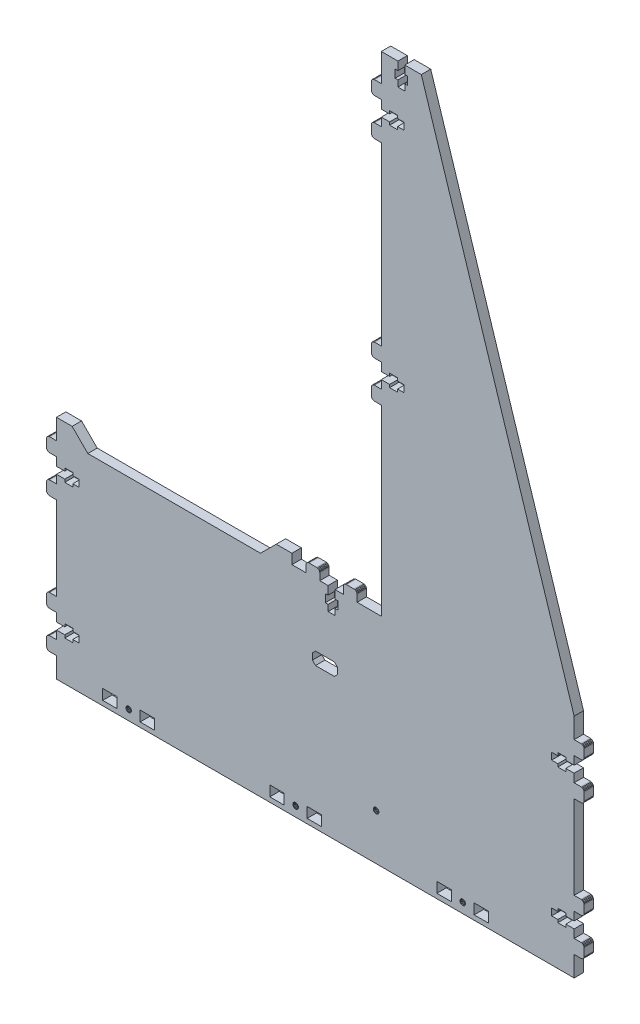
SolidWorks part; units mm, degrees
material "Maple"
ref_plane "Front Plane" through (0, 0, 0) normal (0, 0, 1) x (1, 0, 0)
ref_plane "Top Plane" through (0, 0, 0) normal (0, 1, 0) x (1, 0, 0)
ref_plane "Right Plane" through (0, 0, 0) normal (1, 0, 0) x (0, 0, -1)
sketch "Sketch1" plane through (0, 0, 0) normal (0, 0, 1) x (1, 0, 0)
  line L3039 (22.6213, 221.741) -> (22.6213, 217.341)
  line L3040 (-188.3287, 59.791) -> (-193.4287, 59.791)
  line L3041 (8.2713, 366.6083) -> (13.5713, 366.6083)
  line L3042 (18.6713, 215.541) -> (13.5713, 215.541)
  line L3043 (18.8713, 384.0909) -> (23.2713, 384.0909)
  line L3044 (18.8713, 398.4409) -> (18.8713, 393.1409)
  line L3045 (120.7712, 67.791) -> (125.8712, 67.791)
  line L3046 (125.8712, 67.791) -> (125.8712, 65.991)
  line L3047 (-193.4287, 61.591) -> (-198.7287, 61.591)
  line L3048 (-198.7287, 56.291) -> (-198.7287, 61.591)
  line L3049 (-184.3787, 61.591) -> (-188.3287, 61.591)
  line L3050 (-188.3287, 61.591) -> (-188.3287, 59.791)
  line L3051 (22.6213, 366.6083) -> (22.6213, 362.2083)
  line L3052 (13.5713, 217.341) -> (8.2713, 217.341)
  line L3053 (8.2713, 212.041) -> (3.9713, 212.041)
  line L3054 (120.7712, 59.791) -> (120.7712, 61.591)
  line L3055 (120.7712, 61.591) -> (116.8212, 61.591)
  line L3056 (25.0713, 388.0409) -> (25.0713, 393.1409)
  line L3057 (17.0713, 393.1409) -> (17.0713, 388.0409)
  line L3058 (23.2713, 388.0409) -> (25.0713, 388.0409)
  line L3059 (-193.4287, 67.791) -> (-188.3287, 67.791)
  line L3060 (-188.3287, 67.791) -> (-188.3287, 65.991)
  line L3061 (23.2713, 398.4409) -> (33.7796, 398.4409)
  line L3062 (131.1712, 47.491) -> (135.5212, 47.491)
  line L3063 (18.6713, 366.6083) -> (22.6213, 366.6083)
  line L3064 (18.6713, 217.341) -> (18.6713, 215.541)
  line L3065 (-198.7287, -51.459) -> (-198.7287, -38.459)
  line L3066 (18.6713, 368.4083) -> (18.6713, 366.6083)
  line L3067 (8.2713, 362.2083) -> (8.2713, 356.9083)
  line L3068 (13.5713, 368.4083) -> (18.6713, 368.4083)
  line L3069 (23.2713, 384.0909) -> (23.2713, 388.0409)
  line L3070 (116.8212, 65.991) -> (120.7712, 65.991)
  line L3071 (120.7712, 65.991) -> (120.7712, 67.791)
  line L3072 (8.2713, 380.7083) -> (3.9713, 380.7083)
  line L3073 (13.5713, 223.541) -> (18.6713, 223.541)
  line L3074 (131.1712, 61.591) -> (125.8712, 61.591)
  line L3075 (22.6213, 217.341) -> (18.6713, 217.341)
  line L3076 (13.5713, 366.6083) -> (13.5713, 368.4083)
  line L3077 (-198.7287, 80.091) -> (-198.7287, 93.041)
  line L3078 (-193.4287, 59.791) -> (-193.4287, 61.591)
  line L3079 (13.5713, 362.2083) -> (8.2713, 362.2083)
  line L3080 (8.2713, 356.9083) -> (3.9713, 356.9083)
  line L3081 (131.1712, 56.291) -> (131.1712, 61.591)
  line L3082 (116.8212, 61.591) -> (116.8212, 65.991)
  line L3083 (8.2713, 221.741) -> (13.5713, 221.741)
  line L3084 (8.2713, 235.841) -> (3.9713, 235.841)
  line L3085 (8.2713, 398.4409) -> (18.8713, 398.4409)
  line L3086 (25.0713, 393.1409) -> (23.2713, 393.1409)
  line L3087 (23.2713, 393.1409) -> (23.2713, 398.4409)
  line L3088 (13.5713, 215.541) -> (13.5713, 217.341)
  line L3089 (18.6713, 223.541) -> (18.6713, 221.741)
  line L3090 (-198.7287, 56.291) -> (-203.0787, 56.291)
  line L3091 (-184.3787, 65.991) -> (-184.3787, 61.591)
  line L3092 (8.2713, 217.341) -> (8.2713, 212.041)
  line L3093 (22.6213, 362.2083) -> (18.6713, 362.2083)
  line L3094 (13.5713, 360.4083) -> (13.5713, 362.2083)
  line L3095 (-198.7287, 65.991) -> (-198.7287, 71.291)
  line L3096 (131.1712, 65.991) -> (131.1712, 71.291)
  line L3097 (131.1712, 71.291) -> (135.5212, 71.291)
  line L3098 (131.1712, 47.491) -> (131.1712, -5.859)
  line L3099 (125.8712, 61.591) -> (125.8712, 59.791)
  line L3100 (125.8712, 59.791) -> (120.7712, 59.791)
  line L3101 (131.1712, 80.091) -> (131.1712, 93.041)
  line L3102 (8.2713, 371.9083) -> (8.2713, 366.6083)
  line L3103 (33.7796, 398.4409) -> (131.1712, 93.041)
  line L3104 (18.6713, 221.741) -> (22.6213, 221.741)
  line L3105 (-198.7287, 65.991) -> (-193.4287, 65.991)
  line L3106 (18.8713, 388.0409) -> (18.8713, 384.0909)
  line L3107 (8.2713, 227.041) -> (8.2713, 221.741)
  line L3108 (-188.3287, 65.991) -> (-184.3787, 65.991)
  line L3109 (-48.019, -45.6253) -> (-48.0804, -45.159)
  line L3110 (17.0713, 388.0409) -> (18.8713, 388.0409)
  line L3111 (18.8713, 393.1409) -> (17.0713, 393.1409)
  line L3112 (-193.4287, 65.991) -> (-193.4287, 67.791)
  line L3113 (-198.7287, 80.091) -> (-203.0787, 80.091)
  line L3114 (13.5713, 221.741) -> (13.5713, 223.541)
  line L3115 (125.8712, 65.991) -> (131.1712, 65.991)
  line L3116 (-46.745, -43.4186) -> (-46.2787, -43.3572)
  line L3117 (18.6713, 362.2083) -> (18.6713, 360.4083)
  line L3118 (18.6713, 360.4083) -> (13.5713, 360.4083)
  line L3119 (-25.6287, 86.741) -> (-25.6287, 81.441)
  line L3120 (-21.2287, 72.391) -> (-21.2287, 76.341)
  line L3121 (-21.2287, 81.441) -> (-21.2287, 86.741)
  line L3122 (-15.9287, 86.741) -> (-15.9287, 91.091)
  line L3123 (-48.672, 93.041) -> (-48.672, 86.741)
  line L3124 (-25.6287, 72.391) -> (-21.2287, 72.391)
  line L3125 (-21.2287, 76.341) -> (-19.4287, 76.341)
  line L3126 (-27.4287, 76.341) -> (-25.6287, 76.341)
  line L3127 (-25.6287, 81.441) -> (-27.4287, 81.441)
  line L3128 (-25.6287, 86.741) -> (-30.9287, 86.741)
  line L3129 (-39.7287, 86.741) -> (-39.7287, 91.091)
  line L3130 (-25.6287, 76.341) -> (-25.6287, 72.391)
  line L3131 (-39.7287, 86.741) -> (-48.672, 86.741)
  line L3132 (-19.4287, 81.441) -> (-21.2287, 81.441)
  line L3133 (-15.9287, 86.741) -> (-21.2287, 86.741)
  line L3134 (-27.4287, 81.441) -> (-27.4287, 76.341)
  line L3135 (-19.4287, 76.341) -> (-19.4287, 81.441)
  line L3136 (-48.672, 93.041) -> (-58.672, 93.041)
  line L3137 (3.9713, 212.041) -> (3.4536, 211.9728)
  line L3138 (3.4536, 211.9728) -> (2.9713, 211.773)
  line L3139 (2.9713, 211.773) -> (2.5571, 211.4552)
  line L3140 (2.5571, 211.4552) -> (2.2392, 211.041)
  line L3141 (2.2392, 211.041) -> (2.0394, 210.5586)
  line L3142 (1.9713, 210.041) -> (1.9713, 205.241)
  line L3143 (2.0394, 210.5586) -> (1.9713, 210.041)
  line L3144 (3.9713, 203.241) -> (8.2713, 203.241)
  line L3145 (3.9713, 203.241) -> (3.4536, 203.3091)
  line L3146 (3.4536, 203.3091) -> (2.9713, 203.5089)
  line L3147 (-188.7287, 93.041) -> (-198.7287, 93.041)
  line L3148 (-188.7287, 93.041) -> (-178.7287, 83.041)
  line L3149 (-178.7287, 83.041) -> (-68.672, 83.041)
  line L3150 (-68.672, 83.041) -> (-58.672, 93.041)
  line L3151 (2.9713, 203.5089) -> (2.5571, 203.8268)
  line L3152 (2.5571, 203.8268) -> (2.2392, 204.241)
  line L3153 (2.2392, 204.241) -> (2.0394, 204.7233)
  line L3154 (2.0394, 204.7233) -> (1.9713, 205.241)
  line L3155 (3.9713, 235.841) -> (3.4536, 235.7728)
  line L3156 (3.4536, 235.7728) -> (2.9713, 235.573)
  line L3157 (2.9713, 235.573) -> (2.5571, 235.2552)
  line L3158 (2.5571, 235.2552) -> (2.2392, 234.841)
  line L3159 (2.2392, 234.841) -> (2.0394, 234.3586)
  line L3160 (1.9713, 233.841) -> (1.9713, 229.041)
  line L3161 (2.0394, 234.3586) -> (1.9713, 233.841)
  line L3162 (3.9713, 356.9083) -> (3.4536, 356.8401)
  line L3163 (3.4536, 356.8401) -> (2.9713, 356.6403)
  line L3164 (2.9713, 356.6403) -> (2.5571, 356.3225)
  line L3165 (2.5571, 356.3225) -> (2.2392, 355.9083)
  line L3166 (2.2392, 355.9083) -> (2.0394, 355.4259)
  line L3167 (1.9713, 354.9083) -> (1.9713, 350.1083)
  line L3168 (2.0394, 355.4259) -> (1.9713, 354.9083)
  line L3169 (3.9713, 348.1083) -> (8.2713, 348.1083)
  line L3170 (3.9713, 348.1083) -> (3.4536, 348.1764)
  line L3171 (3.4536, 348.1764) -> (2.9713, 348.3762)
  line L3172 (2.9713, 348.3762) -> (2.5571, 348.6941)
  line L3173 (2.5571, 348.6941) -> (2.2392, 349.1083)
  line L3174 (2.2392, 349.1083) -> (2.0394, 349.5906)
  line L3175 (2.0394, 349.5906) -> (1.9713, 350.1083)
  line L3176 (-205.0787, 78.091) -> (-205.0787, 73.291)
  line L3177 (-205.0787, 78.091) -> (-205.0105, 78.6086)
  line L3178 (-205.0105, 78.6086) -> (-204.8107, 79.091)
  line L3179 (-204.8107, 79.091) -> (-204.4929, 79.5052)
  line L3180 (-204.4929, 79.5052) -> (-204.0787, 79.8231)
  line L3181 (-204.0787, 79.8231) -> (-203.5963, 80.0229)
  line L3182 (-203.5963, 80.0229) -> (-203.0787, 80.091)
  line L3183 (-203.0787, 56.291) -> (-203.5963, 56.2229)
  line L3184 (-203.5963, 56.2229) -> (-204.0787, 56.0231)
  line L3185 (-204.0787, 56.0231) -> (-204.4929, 55.7052)
  line L3186 (-204.4929, 55.7052) -> (-204.8107, 55.291)
  line L3187 (-204.8107, 55.291) -> (-205.0105, 54.8087)
  line L3188 (-205.0787, 54.291) -> (-205.0787, 49.491)
  line L3189 (-205.0105, 54.8087) -> (-205.0787, 54.291)
  line L3190 (-203.0787, 47.491) -> (-198.7287, 47.491)
  line L3191 (-203.0787, 47.491) -> (-203.5963, 47.5592)
  line L3192 (-203.5963, 47.5592) -> (-204.0787, 47.759)
  line L3193 (-204.0787, 47.759) -> (-204.4929, 48.0768)
  line L3194 (-204.4929, 48.0768) -> (-204.8107, 48.491)
  line L3195 (-204.8107, 48.491) -> (-205.0105, 48.9734)
  line L3196 (-205.0105, 48.9734) -> (-205.0787, 49.491)
  line L3197 (3.9713, 380.7083) -> (3.4536, 380.6401)
  line L3198 (3.4536, 380.6401) -> (2.9713, 380.4403)
  line L3199 (2.9713, 380.4403) -> (2.5571, 380.1225)
  line L3200 (2.5571, 380.1225) -> (2.2392, 379.7083)
  line L3201 (2.2392, 379.7083) -> (2.0394, 379.2259)
  line L3202 (1.9713, 378.7083) -> (1.9713, 373.9083)
  line L3203 (2.0394, 379.2259) -> (1.9713, 378.7083)
  line L3204 (3.9713, 371.9083) -> (8.2713, 371.9083)
  line L3205 (3.9713, 371.9083) -> (3.4536, 371.9764)
  line L3206 (3.4536, 371.9764) -> (2.9713, 372.1762)
  line L3207 (2.9713, 372.1762) -> (2.5571, 372.4941)
  line L3208 (2.5571, 372.4941) -> (2.2392, 372.9083)
  line L3209 (2.2392, 372.9083) -> (2.0394, 373.3906)
  line L3210 (2.0394, 373.3906) -> (1.9713, 373.9083)
  line L3211 (3.9713, 227.041) -> (8.2713, 227.041)
  line L3212 (3.9713, 227.041) -> (3.4536, 227.1091)
  line L3213 (3.4536, 227.1091) -> (2.9713, 227.3089)
  line L3214 (2.9713, 227.3089) -> (2.5571, 227.6267)
  line L3215 (2.5571, 227.6267) -> (2.2392, 228.041)
  line L3216 (2.2392, 228.041) -> (2.0394, 228.5233)
  line L3217 (2.0394, 228.5233) -> (1.9713, 229.041)
  line L3218 (-203.0787, 71.291) -> (-198.7287, 71.291)
  line L3219 (-203.0787, 71.291) -> (-203.5963, 71.3592)
  line L3220 (-203.5963, 71.3592) -> (-204.0787, 71.559)
  line L3221 (-204.0787, 71.559) -> (-204.4929, 71.8768)
  line L3222 (-204.4929, 71.8768) -> (-204.8107, 72.291)
  line L3223 (-204.8107, 72.291) -> (-205.0105, 72.7734)
  line L3224 (-205.0105, 72.7734) -> (-205.0787, 73.291)
  line L3225 (135.5212, 71.291) -> (136.0389, 71.3592)
  line L3226 (136.0389, 71.3592) -> (136.5212, 71.559)
  line L3227 (136.5212, 71.559) -> (136.9354, 71.8768)
  line L3228 (136.9354, 71.8768) -> (137.2533, 72.291)
  line L3229 (137.2533, 72.291) -> (137.4531, 72.7734)
  line L3230 (137.5212, 73.291) -> (137.5212, 78.091)
  line L3231 (137.4531, 72.7734) -> (137.5212, 73.291)
  line L3232 (135.5212, 80.091) -> (131.1712, 80.091)
  line L3233 (135.5212, 80.091) -> (136.0389, 80.0229)
  line L3234 (136.0389, 80.0229) -> (136.5212, 79.8231)
  line L3235 (136.5212, 79.8231) -> (136.9354, 79.5052)
  line L3236 (136.9354, 79.5052) -> (137.2533, 79.091)
  line L3237 (137.2533, 79.091) -> (137.4531, 78.6087)
  line L3238 (137.4531, 78.6087) -> (137.5212, 78.091)
  line L3239 (-30.9287, 91.091) -> (-30.9287, 86.741)
  line L3240 (-30.9287, 91.091) -> (-30.9969, 91.6086)
  line L3241 (-30.9969, 91.6086) -> (-31.1967, 92.091)
  line L3242 (-31.1967, 92.091) -> (-31.5145, 92.5052)
  line L3243 (-31.5145, 92.5052) -> (-31.9287, 92.8231)
  line L3244 (-31.9287, 92.8231) -> (-32.4111, 93.0229)
  line L3245 (-32.4111, 93.0229) -> (-32.9287, 93.091)
  line L3246 (-15.9287, 91.091) -> (-15.8606, 91.6086)
  line L3247 (-15.8606, 91.6086) -> (-15.6608, 92.091)
  line L3248 (-15.6608, 92.091) -> (-15.3429, 92.5052)
  line L3249 (-15.3429, 92.5052) -> (-14.9287, 92.8231)
  line L3250 (-14.9287, 92.8231) -> (-14.4464, 93.0229)
  line L3251 (-13.9287, 93.091) -> (-9.1287, 93.091)
  line L3252 (-14.4464, 93.0229) -> (-13.9287, 93.091)
  line L3253 (-39.7287, 91.091) -> (-39.6606, 91.6086)
  line L3254 (-39.6606, 91.6086) -> (-39.4608, 92.091)
  line L3255 (-39.4608, 92.091) -> (-39.1429, 92.5052)
  line L3256 (-39.1429, 92.5052) -> (-38.7287, 92.8231)
  line L3257 (-38.7287, 92.8231) -> (-38.2463, 93.0229)
  line L3258 (-37.7287, 93.091) -> (-32.9287, 93.091)
  line L3259 (-38.2463, 93.0229) -> (-37.7287, 93.091)
  line L3260 (-7.1287, 91.091) -> (-7.1287, 86.741)
  line L3261 (-7.1287, 91.091) -> (-7.1969, 91.6086)
  line L3262 (-7.1969, 91.6086) -> (-7.3967, 92.091)
  line L3263 (-7.3967, 92.091) -> (-7.7145, 92.5052)
  line L3264 (-7.7145, 92.5052) -> (-8.1287, 92.8231)
  line L3265 (-8.1287, 92.8231) -> (-8.6111, 93.0229)
  line L3266 (-8.6111, 93.0229) -> (-9.1287, 93.091)
  line L3267 (135.5212, 47.491) -> (136.0389, 47.5592)
  line L3268 (136.0389, 47.5592) -> (136.5212, 47.759)
  line L3269 (136.5212, 47.759) -> (136.9354, 48.0768)
  line L3270 (136.9354, 48.0768) -> (137.2533, 48.491)
  line L3271 (137.2533, 48.491) -> (137.4531, 48.9734)
  line L3272 (137.5212, 49.491) -> (137.5212, 54.291)
  line L3273 (137.4531, 48.9734) -> (137.5212, 49.491)
  line L3274 (135.5212, 56.291) -> (131.1712, 56.291)
  line L3275 (135.5212, 56.291) -> (136.0389, 56.2229)
  line L3276 (136.0389, 56.2229) -> (136.5212, 56.0231)
  line L3277 (136.5212, 56.0231) -> (136.9354, 55.7052)
  line L3278 (136.9354, 55.7052) -> (137.2533, 55.291)
  line L3279 (137.2533, 55.291) -> (137.4531, 54.8087)
  line L3280 (137.4531, 54.8087) -> (137.5212, 54.291)
  line L3281 (61.7316, -46.0598) -> (61.4453, -46.433)
  line L3282 (-53.5787, -48.459) -> (-62.7787, -48.459)
  line L3283 (52.8713, -41.859) -> (52.8713, -48.459)
  line L3284 (67.4713, -48.459) -> (67.4713, -41.859)
  line L3285 (52.8713, -48.459) -> (43.6713, -48.459)
  line L3286 (-151.8278, -46.7193) -> (-152.2624, -46.8993)
  line L3287 (-152.2624, -46.8993) -> (-152.7287, -46.9607)
  line L3288 (61.0721, -46.7193) -> (60.6376, -46.8993)
  line L3289 (-153.195, -46.8993) -> (-153.6295, -46.7193)
  line L3290 (-153.6295, -43.5986) -> (-153.195, -43.4186)
  line L3291 (-62.7787, -41.859) -> (-53.5787, -41.859)
  line L3292 (-44.7184, -46.0598) -> (-45.0047, -46.433)
  line L3293 (-46.2787, -46.9607) -> (-46.745, -46.8993)
  line L3294 (-154.5304, -45.159) -> (-154.469, -44.6927)
  line L3295 (-151.4547, -43.885) -> (-151.1683, -44.2581)
  line L3296 (61.973, -45.159) -> (61.9116, -45.6253)
  line L3297 (76.6713, -48.459) -> (67.4713, -48.459)
  line L3298 (61.9116, -44.6927) -> (61.973, -45.159)
  line L3299 (59.7049, -43.4186) -> (60.1713, -43.3572)
  line L3300 (-136.2287, -41.859) -> (-136.2287, -48.459)
  line L3301 (-151.4547, -46.433) -> (-151.8278, -46.7193)
  line L3302 (-169.2287, -41.859) -> (-160.0287, -41.859)
  line L3303 (-153.6295, -46.7193) -> (-154.0027, -46.433)
  line L3304 (-145.4287, -48.459) -> (-145.4287, -41.859)
  line L3305 (-136.2287, -48.459) -> (-145.4287, -48.459)
  line L3306 (58.4309, -45.6253) -> (58.3695, -45.159)
  line L3307 (60.1713, -46.9607) -> (59.7049, -46.8993)
  line L3308 (-160.0287, -48.459) -> (-169.2287, -48.459)
  line L3309 (59.2704, -46.7193) -> (58.8972, -46.433)
  line L3310 (59.7049, -46.8993) -> (59.2704, -46.7193)
  line L3311 (-38.9787, -41.859) -> (-29.7787, -41.859)
  line L3312 (-29.7787, -48.459) -> (-38.9787, -48.459)
  line L3313 (-53.5787, -41.859) -> (-53.5787, -48.459)
  line L3314 (-47.1796, -43.5986) -> (-46.745, -43.4186)
  line L3315 (-152.7287, -46.9607) -> (-153.195, -46.8993)
  line L3316 (-152.2624, -43.4186) -> (-151.8278, -43.5986)
  line L3317 (61.7316, -44.2581) -> (61.9116, -44.6927)
  line L3318 (61.4453, -43.885) -> (61.7316, -44.2581)
  line L3319 (61.0721, -43.5986) -> (61.4453, -43.885)
  line L3320 (60.1713, -43.3572) -> (60.6376, -43.4186)
  line L3321 (-48.0804, -45.159) -> (-48.019, -44.6927)
  line L3322 (-48.019, -44.6927) -> (-47.839, -44.2581)
  line L3323 (-47.5527, -43.885) -> (-47.1796, -43.5986)
  line L3324 (-44.5384, -44.6927) -> (-44.477, -45.159)
  line L3325 (-45.3778, -46.7193) -> (-45.8124, -46.8993)
  line L3326 (-45.8124, -46.8993) -> (-46.2787, -46.9607)
  line L3327 (-47.1796, -46.7193) -> (-47.5527, -46.433)
  line L3328 (59.2704, -43.5986) -> (59.7049, -43.4186)
  line L3329 (-154.469, -44.6927) -> (-154.289, -44.2581)
  line L3330 (-154.289, -44.2581) -> (-154.0027, -43.885)
  line L3331 (-150.9883, -45.6253) -> (-151.1683, -46.0598)
  line L3332 (-145.4287, -41.859) -> (-136.2287, -41.859)
  line L3333 (-38.9787, -48.459) -> (-38.9787, -41.859)
  line L3334 (-203.0787, -29.659) -> (-203.5963, -29.7271)
  line L3335 (-198.7287, -5.859) -> (-203.0787, -5.859)
  line L3336 (-188.3287, -24.359) -> (-188.3287, -26.159)
  line L3337 (-188.3287, -26.159) -> (-193.4287, -26.159)
  line L3338 (-203.0787, -38.459) -> (-198.7287, -38.459)
  line L3339 (-204.8107, -6.859) -> (-204.4929, -6.4448)
  line L3340 (-205.0787, -7.859) -> (-205.0105, -7.3413)
  line L3341 (-204.0787, -29.9269) -> (-204.4929, -30.2448)
  line L3342 (-198.7287, -19.959) -> (-193.4287, -19.959)
  line L3343 (-205.0105, -7.3413) -> (-204.8107, -6.859)
  line L3344 (-204.4929, -30.2448) -> (-204.8107, -30.659)
  line L3345 (-204.4929, -37.8732) -> (-204.8107, -37.459)
  line L3346 (-193.4287, -24.359) -> (-198.7287, -24.359)
  line L3347 (-184.3787, -24.359) -> (-188.3287, -24.359)
  line L3348 (-203.5963, -5.9271) -> (-203.0787, -5.859)
  line L3349 (-198.7287, -29.659) -> (-203.0787, -29.659)
  line L3350 (-203.0787, -38.459) -> (-203.5963, -38.3908)
  line L3351 (-204.0787, -6.1269) -> (-203.5963, -5.9271)
  line L3352 (-193.4287, -19.959) -> (-193.4287, -18.159)
  line L3353 (-203.5963, -29.7271) -> (-204.0787, -29.9269)
  line L3354 (-203.0787, -14.659) -> (-198.7287, -14.659)
  line L3355 (-203.5963, -38.3908) -> (-204.0787, -38.191)
  line L3356 (-205.0105, -13.1766) -> (-205.0787, -12.659)
  line L3357 (-204.8107, -13.659) -> (-205.0105, -13.1766)
  line L3358 (-204.4929, -14.0732) -> (-204.8107, -13.659)
  line L3359 (-188.3287, -19.959) -> (-184.3787, -19.959)
  line L3360 (-184.3787, -19.959) -> (-184.3787, -24.359)
  line L3361 (-193.4287, -18.159) -> (-188.3287, -18.159)
  line L3362 (-205.0787, -31.659) -> (-205.0787, -36.459)
  line L3363 (-204.0787, -14.391) -> (-204.4929, -14.0732)
  line L3364 (-203.5963, -14.5908) -> (-204.0787, -14.391)
  line L3365 (-203.0787, -14.659) -> (-203.5963, -14.5908)
  line L3366 (-205.0105, -31.1413) -> (-205.0787, -31.659)
  line L3367 (-204.0787, -38.191) -> (-204.4929, -37.8732)
  line L3368 (-193.4287, -26.159) -> (-193.4287, -24.359)
  line L3369 (-205.0787, -7.859) -> (-205.0787, -12.659)
  line L3370 (-205.0105, -36.9766) -> (-205.0787, -36.459)
  line L3371 (-204.8107, -37.459) -> (-205.0105, -36.9766)
  line L3372 (-204.4929, -6.4448) -> (-204.0787, -6.1269)
  line L3373 (-204.8107, -30.659) -> (-205.0105, -31.1413)
  line L3374 (-188.3287, -18.159) -> (-188.3287, -19.959)
  line L3375 (-198.7287, -5.859) -> (-198.7287, 47.491)
  line L3376 (-198.7287, -29.659) -> (-198.7287, -24.359)
  line L3377 (-198.7287, -19.959) -> (-198.7287, -14.659)
  line L3378 (137.2533, -13.659) -> (137.4531, -13.1766)
  line L3379 (136.9354, -14.0732) -> (137.2533, -13.659)
  line L3380 (136.5212, -14.391) -> (136.9354, -14.0732)
  line L3381 (136.0389, -14.5908) -> (136.5212, -14.391)
  line L3382 (135.5212, -14.659) -> (136.0389, -14.5908)
  line L3383 (125.8712, -24.359) -> (125.8712, -26.159)
  line L3384 (137.4531, -7.3413) -> (137.5212, -7.859)
  line L3385 (137.2533, -6.859) -> (137.4531, -7.3413)
  line L3386 (120.7712, -24.359) -> (116.8212, -24.359)
  line L3387 (125.8712, -19.959) -> (131.1712, -19.959)
  line L3388 (131.1712, -24.359) -> (125.8712, -24.359)
  line L3389 (125.8712, -18.159) -> (125.8712, -19.959)
  line L3390 (136.9354, -30.2448) -> (137.2533, -30.659)
  line L3391 (137.2533, -30.659) -> (137.4531, -31.1413)
  line L3392 (137.4531, -31.1413) -> (137.5212, -31.659)
  line L3393 (125.8712, -26.159) -> (120.7712, -26.159)
  line L3394 (116.8212, -24.359) -> (116.8212, -19.959)
  line L3395 (135.5212, -38.459) -> (136.0389, -38.3908)
  line L3396 (136.0389, -5.9271) -> (136.5212, -6.1269)
  line L3397 (120.7712, -18.159) -> (125.8712, -18.159)
  line L3398 (131.1712, -38.459) -> (135.5212, -38.459)
  line L3399 (116.8212, -19.959) -> (120.7712, -19.959)
  line L3400 (137.4531, -36.9766) -> (137.5212, -36.459)
  line L3401 (135.5212, -29.659) -> (131.1712, -29.659)
  line L3402 (135.5212, -29.659) -> (136.0389, -29.7271)
  line L3403 (120.7712, -19.959) -> (120.7712, -18.159)
  line L3404 (131.1712, -14.659) -> (135.5212, -14.659)
  line L3405 (135.5212, -5.859) -> (136.0389, -5.9271)
  line L3406 (135.5212, -5.859) -> (131.1712, -5.859)
  line L3407 (137.4531, -13.1766) -> (137.5212, -12.659)
  line L3408 (137.5212, -12.659) -> (137.5212, -7.859)
  line L3409 (136.0389, -29.7271) -> (136.5212, -29.9269)
  line L3410 (136.5212, -29.9269) -> (136.9354, -30.2448)
  line L3411 (136.0389, -38.3908) -> (136.5212, -38.191)
  line L3412 (136.5212, -38.191) -> (136.9354, -37.8732)
  line L3413 (136.9354, -37.8732) -> (137.2533, -37.459)
  line L3414 (137.2533, -37.459) -> (137.4531, -36.9766)
  line L3415 (137.5212, -36.459) -> (137.5212, -31.659)
  line L3416 (120.7712, -26.159) -> (120.7712, -24.359)
  line L3417 (136.9354, -6.4448) -> (137.2533, -6.859)
  line L3418 (136.5212, -6.1269) -> (136.9354, -6.4448)
  line L3419 (131.1712, -14.659) -> (131.1712, -19.959)
  line L3420 (131.1712, -24.359) -> (131.1712, -29.659)
  line L3421 (131.1712, -38.459) -> (131.1712, -51.459)
  line L3422 (-44.7184, -44.2581) -> (-44.5384, -44.6927)
  line L3423 (76.6713, -41.859) -> (76.6713, -48.459)
  line L3424 (58.6109, -44.2581) -> (58.8972, -43.885)
  line L3425 (-47.839, -46.0598) -> (-48.019, -45.6253)
  line L3426 (43.6713, -41.859) -> (52.8713, -41.859)
  line L3427 (-169.2287, -48.459) -> (-169.2287, -41.859)
  line L3428 (-154.289, -46.0598) -> (-154.469, -45.6253)
  line L3429 (-151.8278, -43.5986) -> (-151.4547, -43.885)
  line L3430 (-29.7787, -41.859) -> (-29.7787, -48.459)
  line L3431 (-46.2787, -43.3572) -> (-45.8124, -43.4186)
  line L3432 (-44.477, -45.159) -> (-44.5384, -45.6253)
  line L3433 (-62.7787, -48.459) -> (-62.7787, -41.859)
  line L3434 (-46.745, -46.8993) -> (-47.1796, -46.7193)
  line L3435 (-47.839, -44.2581) -> (-47.5527, -43.885)
  line L3436 (-151.1683, -46.0598) -> (-151.4547, -46.433)
  line L3437 (-47.5527, -46.433) -> (-47.839, -46.0598)
  line L3438 (-154.0027, -43.885) -> (-153.6295, -43.5986)
  line L3439 (-45.0047, -43.885) -> (-44.7184, -44.2581)
  line L3440 (-45.3778, -43.5986) -> (-45.0047, -43.885)
  line L3441 (-150.9269, -45.159) -> (-150.9883, -45.6253)
  line L3442 (61.4453, -46.433) -> (61.0721, -46.7193)
  line L3443 (43.6713, -48.459) -> (43.6713, -41.859)
  line L3444 (67.4713, -41.859) -> (76.6713, -41.859)
  line L3445 (-45.8124, -43.4186) -> (-45.3778, -43.5986)
  line L3446 (61.9116, -45.6253) -> (61.7316, -46.0598)
  line L3447 (-153.195, -43.4186) -> (-152.7287, -43.3572)
  line L3448 (-151.1683, -44.2581) -> (-150.9883, -44.6927)
  line L3449 (58.6109, -46.0598) -> (58.4309, -45.6253)
  line L3450 (58.8972, -46.433) -> (58.6109, -46.0598)
  line L3451 (58.3695, -45.159) -> (58.4309, -44.6927)
  line L3452 (-154.469, -45.6253) -> (-154.5304, -45.159)
  line L3453 (-44.5384, -45.6253) -> (-44.7184, -46.0598)
  line L3454 (-45.0047, -46.433) -> (-45.3778, -46.7193)
  line L3455 (-160.0287, -41.859) -> (-160.0287, -48.459)
  line L3456 (-154.0027, -46.433) -> (-154.289, -46.0598)
  line L3457 (60.6376, -46.8993) -> (60.1713, -46.9607)
  line L3458 (58.8972, -43.885) -> (59.2704, -43.5986)
  line L3459 (60.6376, -43.4186) -> (61.0721, -43.5986)
  line L3460 (-150.9883, -44.6927) -> (-150.9269, -45.159)
  line L3461 (58.4309, -44.6927) -> (58.6109, -44.2581)
  line L3462 (-152.7287, -43.3572) -> (-152.2624, -43.4186)
  line L3463 (6.7713, -22.159) -> (6.7099, -22.6249)
  line L3464 (6.7099, -22.6249) -> (6.5301, -23.059)
  line L3465 (6.5301, -23.059) -> (6.2441, -23.4318)
  line L3466 (6.2441, -23.4318) -> (5.8713, -23.7178)
  line L3467 (5.8713, -23.7178) -> (5.4372, -23.8976)
  line L3468 (5.4372, -23.8976) -> (4.9713, -23.959)
  line L3469 (4.9713, -23.959) -> (4.5054, -23.8976)
  line L3470 (4.5054, -23.8976) -> (4.0713, -23.7178)
  line L3471 (4.0713, -23.7178) -> (3.6985, -23.4318)
  line L3472 (3.6985, -23.4318) -> (3.4124, -23.059)
  line L3473 (3.4124, -23.059) -> (3.2326, -22.6249)
  line L3474 (3.2326, -22.6249) -> (3.1713, -22.159)
  line L3475 (3.1713, -22.159) -> (3.2326, -21.6931)
  line L3476 (3.2326, -21.6931) -> (3.4124, -21.259)
  line L3477 (3.4124, -21.259) -> (3.6985, -20.8862)
  line L3478 (3.6985, -20.8862) -> (4.0713, -20.6001)
  line L3479 (4.0713, -20.6001) -> (4.5054, -20.4203)
  line L3480 (4.5054, -20.4203) -> (4.9713, -20.359)
  line L3481 (4.9713, -20.359) -> (5.4372, -20.4203)
  line L3482 (5.4372, -20.4203) -> (5.8713, -20.6001)
  line L3483 (5.8713, -20.6001) -> (6.2441, -20.8862)
  line L3484 (6.2441, -20.8862) -> (6.5301, -21.259)
  line L3485 (6.5301, -21.259) -> (6.7099, -21.6931)
  line L3486 (6.7099, -21.6931) -> (6.7713, -22.159)
  line L3487 (-19.6307, 44.5778) -> (-21.6307, 46.5778)
  line L3488 (-35.6267, 44.5778) -> (-33.6267, 46.5778)
  line L3489 (-21.6307, 38.5778) -> (-19.6307, 40.5778)
  line L3490 (-35.6267, 44.5778) -> (-35.6267, 40.5778)
  line L3491 (-33.6267, 46.5778) -> (-21.6307, 46.5778)
  line L3492 (-19.6307, 40.5778) -> (-19.6307, 44.5778)
  line L3493 (-33.6267, 38.5778) -> (-21.6307, 38.5778)
  line L3494 (-35.6267, 40.5778) -> (-33.6267, 38.5778)
  line L8404 (8.2713, 380.7083) -> (8.2713, 398.4409)
  line L8405 (8.2713, 86.741) -> (8.2713, 203.241)
  line L8406 (-198.7287, -51.459) -> (131.1712, -51.459)
  line L8407 (8.2713, 348.1083) -> (8.2713, 235.841)
  line L8408 (-7.1287, 86.741) -> (8.2713, 86.741)
  line L9236 (122.6956, -44.9271) -> (122.6956, -45.233)
  line L9237 (122.6956, -45.233) -> (122.6753, -45.3294)
  line L9238 (122.6753, -45.3294) -> (122.6144, -45.4188)
  line L9239 (122.6144, -45.4188) -> (122.3709, -45.5764)
  line L9240 (122.3709, -45.5764) -> (122.015, -45.6794)
  line L9241 (122.015, -45.6794) -> (121.5717, -45.7138)
  line L9242 (121.5717, -45.7138) -> (121.1268, -45.6794)
  line L9243 (121.1268, -45.6794) -> (120.7663, -45.5764)
  line L9244 (120.7663, -45.5764) -> (120.5274, -45.4219)
  line L9245 (120.5274, -45.4219) -> (120.4677, -45.3317)
  line L9246 (120.4677, -45.3317) -> (120.4478, -45.233)
  line L9247 (120.4478, -45.233) -> (120.4478, -41.8866)
  line L9248 (120.4478, -41.8866) -> (120.4677, -41.7906)
  line L9249 (120.4677, -41.7906) -> (120.5274, -41.7024)
  line L9250 (120.5274, -41.7024) -> (120.7663, -41.5494)
  line L9251 (120.7663, -41.5494) -> (121.1331, -41.4417)
  line L9252 (121.1331, -41.4417) -> (121.5717, -41.4058)
  line L9253 (121.5717, -41.4058) -> (122.0056, -41.4417)
  line L9254 (122.0056, -41.4417) -> (122.3709, -41.5494)
  line L9255 (122.3709, -41.5494) -> (122.6144, -41.7055)
  line L9256 (122.6144, -41.7055) -> (122.6753, -41.7929)
  line L9257 (122.6753, -41.7929) -> (122.6956, -41.8866)
  line L9258 (122.6956, -41.8866) -> (122.6956, -42.1925)
  line L9259 (122.6956, -42.1925) -> (122.6956, -41.8866)
  line L9260 (122.6956, -41.8866) -> (122.6753, -41.7929)
  line L9261 (122.6753, -41.7929) -> (122.6144, -41.7055)
  line L9262 (122.6144, -41.7055) -> (122.3709, -41.5494)
  line L9263 (122.3709, -41.5494) -> (122.0056, -41.4417)
  line L9264 (122.0056, -41.4417) -> (121.5717, -41.4058)
  line L9265 (121.5717, -41.4058) -> (121.1331, -41.4417)
  line L9266 (121.1331, -41.4417) -> (120.7663, -41.5494)
  line L9267 (120.7663, -41.5494) -> (120.5274, -41.7024)
  line L9268 (120.5274, -41.7024) -> (120.4677, -41.7906)
  line L9269 (120.4677, -41.7906) -> (120.4478, -41.8866)
  line L9270 (120.4478, -41.8866) -> (120.4478, -45.233)
  line L9271 (120.4478, -45.233) -> (120.4677, -45.3317)
  line L9272 (120.4677, -45.3317) -> (120.5274, -45.4219)
  line L9273 (120.5274, -45.4219) -> (120.7663, -45.5764)
  line L9274 (120.7663, -45.5764) -> (121.1268, -45.6794)
  line L9275 (121.1268, -45.6794) -> (121.5717, -45.7138)
  line L9276 (121.5717, -45.7138) -> (122.015, -45.6794)
  line L9277 (122.015, -45.6794) -> (122.3709, -45.5764)
  line L9278 (122.3709, -45.5764) -> (122.6144, -45.4188)
  line L9279 (122.6144, -45.4188) -> (122.6753, -45.3294)
  line L9280 (122.6753, -45.3294) -> (122.6956, -45.233)
  line L9281 (122.6956, -45.233) -> (122.6956, -44.9271)
extrude "Boss-Extrude1" add sketch "Sketch1" along normal blind 6
